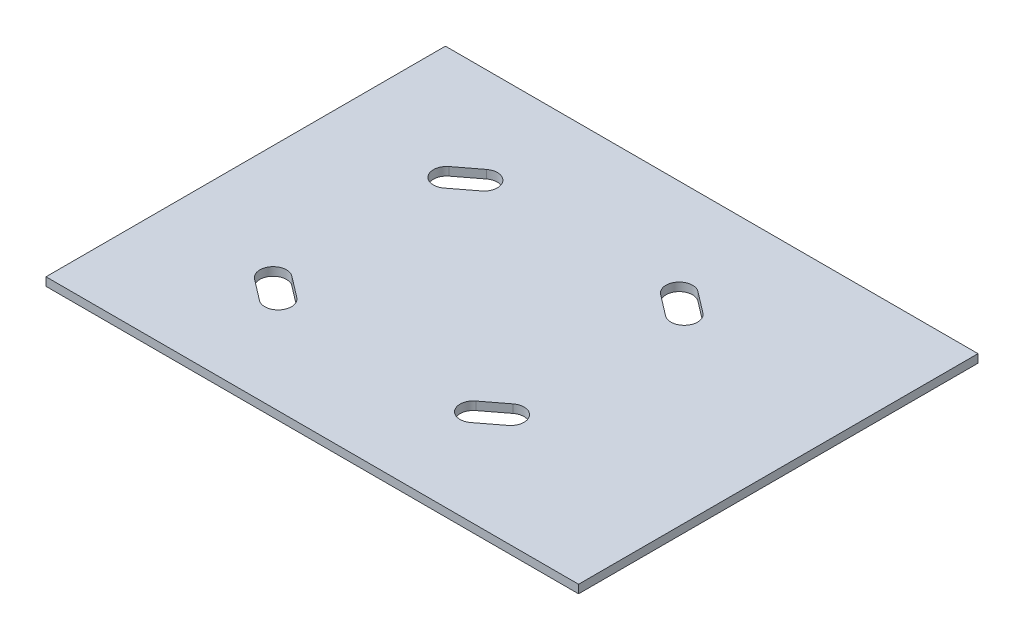
SolidWorks part; units mm, degrees
ref_plane "Front Plane" through (0, 0, 0) normal (0, 0, 1) x (1, 0, 0)
ref_plane "Top Plane" through (0, 0, 0) normal (0, 1, 0) x (1, 0, 0)
ref_plane "Right Plane" through (0, 0, 0) normal (1, 0, 0) x (0, 0, -1)
sketch "Sketch1" plane through (0, 0, 0) normal (0, 1, 0) x (1, 0, 0)
  line L0 (-69.85, 0) -> (69.85, 0) construction
  line L1 (69.85, 50.8) -> (-69.85, 50.8) construction
  line L2 (69.85, 50.8) -> (69.85, -50.8) construction
  line L3 (69.85, -50.8) -> (-69.85, -50.8) construction
  line L4 (-69.85, 50.8) -> (-69.85, -50.8) construction
  line L5 (69.85, 50.8) -> (-69.85, -50.8) construction
  line L6 (69.85, -50.8) -> (-69.85, 50.8) construction
  line L7 (0, 50.8) -> (0, -50.8) construction
  line L8 (-52.07, 50.8) -> (-52.07, -50.8) construction
  line L9 (52.07, 50.8) -> (52.07, -50.8) construction
  line L10 (-30.48, 50.8) -> (-30.48, -50.8) construction
  line L11 (30.48, 50.8) -> (30.48, -50.8) construction
  line L12 (-69.85, 27.94) -> (69.85, 27.94) construction
  line L13 (-69.85, 44.45) -> (69.85, 44.45) construction
  line L14 (-52.07, 27.94) -> (-30.48, 44.45) construction
  line L15 (-52.07, 44.45) -> (-30.48, 27.94) construction
  line L16 (-33.2043, 42.3667) -> (-49.3457, 30.0233) construction
  line L17 (-46.2598, 25.988) -> (-30.1185, 38.3314) construction
  line L18 (-46.2598, 25.988) -> (-52.4315, 34.0586) construction
  line L19 (-30.1185, 38.3314) -> (-36.2902, 46.402) construction
  line L20 (-52.4315, 34.0586) -> (-36.2902, 46.402) construction
  line L21 (-46.2598, 25.988) -> (-36.2902, 46.402) construction
  line L22 (-30.1185, 38.3314) -> (-52.4315, 34.0586) construction
  line L23 (-40.3255, 43.3162) -> (-34.1538, 35.2455) construction
  line L24 (-48.3962, 37.1445) -> (-42.2245, 29.0738) construction
  line L25 (-48.3962, 37.1445) -> (-40.3255, 43.3162)
  line L26 (-34.1538, 35.2455) -> (-42.2245, 29.0738)
  line L27 (34.1538, 35.2455) -> (42.2245, 29.0738)
  line L28 (48.3962, 37.1445) -> (40.3255, 43.3162)
  line L29 (34.1538, -35.2455) -> (42.2245, -29.0738)
  line L30 (48.3962, -37.1445) -> (40.3255, -43.3162)
  line L31 (-48.3962, -37.1445) -> (-40.3255, -43.3162)
  line L32 (-34.1538, -35.2455) -> (-42.2245, -29.0738)
  line L33 (-187.6556, 0) -> (294.8204, 0) construction
  line L34 (114.3, -76.2) -> (-88.9, -76.2)
  line L35 (114.3, -76.2) -> (114.3, 76.2)
  line L36 (114.3, 76.2) -> (-88.9, 76.2)
  line L37 (-88.9, -76.2) -> (-88.9, 76.2)
  line L38 (114.3, -76.2) -> (-88.9, 76.2) construction
  line L39 (114.3, 76.2) -> (-88.9, -76.2) construction
  arc A0 (-40.3255, 43.3162) -> (-34.1538, 35.2455) centre (-37.2397, 39.2808) cw
  arc A1 (-48.3962, 37.1445) -> (-42.2245, 29.0738) centre (-45.3103, 33.1092) ccw
  arc A2 (48.3962, 37.1445) -> (42.2245, 29.0738) centre (45.3103, 33.1092) cw
  arc A3 (40.3255, 43.3162) -> (34.1538, 35.2455) centre (37.2397, 39.2808) ccw
  arc A4 (48.3962, -37.1445) -> (42.2245, -29.0738) centre (45.3103, -33.1092) ccw
  arc A5 (40.3255, -43.3162) -> (34.1538, -35.2455) centre (37.2397, -39.2808) cw
  arc A6 (-48.3962, -37.1445) -> (-42.2245, -29.0738) centre (-45.3103, -33.1092) cw
  arc A7 (-40.3255, -43.3162) -> (-34.1538, -35.2455) centre (-37.2397, -39.2808) ccw
  point P0 (0, 0)
  point P26 (-41.275, 36.195)
  point P30 (-41.275, 36.195)
  point P37 (12.7, 0)
  dimension "D1" = 101.6
  dimension "D2" = 139.7
  dimension "D3" = 17.78
  dimension "D4" = 17.78
  dimension "D5" = 39.37
  dimension "D6" = 22.86
  dimension "D7" = 6.35
  dimension "D8" = 20.32
  dimension "D9" = 10.16
  dimension "D10" = 5.08
  dimension "D11" = 5.08
  dimension "D12" = 203.2
  dimension "D13" = 152.4
  dimension "D14" = 12.7
  dimension "D15" = 203.2
extrude "Boss-Extrude1" add sketch "Sketch1" along normal blind 3.175 contours L1 L4 L3 L2 A7 L31 A6 L32 A1 L25 A0 L26 A3 L28 A2 L27 L30 A5 L29 A4
